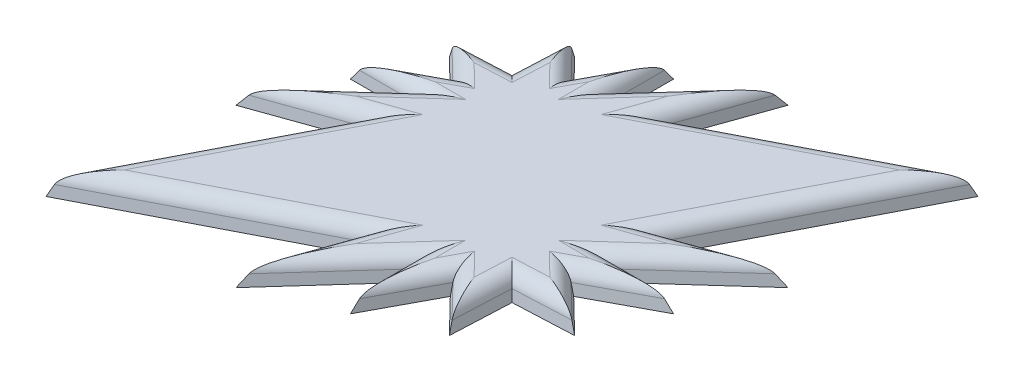
SolidWorks part; units mm, degrees
material "ABS"
ref_plane "Front Plane" through (0, 0, 0) normal (0, 0, 1) x (1, 0, 0)
ref_plane "Top Plane" through (0, 0, 0) normal (0, 1, 0) x (1, 0, 0)
ref_plane "Right Plane" through (0, 0, 0) normal (1, 0, 0) x (0, 0, -1)
sketch "Sketch1" plane through (0, 0, 0) normal (0, 1, 0) x (1, 0, 0)
  line L1 (-17.5, 17.5) -> (17.5, 17.5)
  line L2 (-17.5, 17.5) -> (-17.5, -17.5)
  line L3 (-17.5, -17.5) -> (17.5, -17.5)
  line L4 (17.5, 17.5) -> (17.5, -17.5)
  line L5 (-17.5, 17.5) -> (17.5, -17.5) construction
  line L6 (-17.5, -17.5) -> (17.5, 17.5) construction
  point P0 (0, 0)
  dimension "D1" = 35
sketch "Sketch2" plane through (0, 0, 0) normal (0, 1, 0) x (1, 0, 0)
  line L0 (0, 0) -> (15.1654, 15.1654) construction
  line L1 (-17.5, -17.5) -> (17.5, 17.5) construction
  line L2 (15.1654, 15.1654) -> (1.7587, 8.275)
  line L3 (1.7587, 8.275) -> (3.8411, 14.1232)
  line L4 (3.8411, 14.1232) -> (-1.3581, 8.3501)
  line L5 (-1.3581, 8.3501) -> (-1.3581, 11.8764)
  line L6 (-1.3581, 11.8764) -> (-3.6265, 7.6432)
  line L7 (-3.6265, 7.6432) -> (-5.8041, 9.8791)
  line L8 (-5.8041, 9.8791) -> (-5.982, 5.982)
  line L9 (-17.5, 17.5) -> (17.5, -17.5) construction
  line L10 (9.8791, -5.8041) -> (5.982, -5.982)
  line L11 (7.6432, -3.6265) -> (9.8791, -5.8041)
  line L12 (11.8764, -1.3581) -> (7.6432, -3.6265)
  line L13 (8.3501, -1.3581) -> (11.8764, -1.3581)
  line L14 (14.1232, 3.8411) -> (8.3501, -1.3581)
  line L15 (8.275, 1.7587) -> (14.1232, 3.8411)
  line L16 (15.1654, 15.1654) -> (8.275, 1.7587)
  line L17 (-17.5, 17.5) -> (17.5, -17.5) construction
  line L18 (5.8041, -9.8791) -> (5.982, -5.982)
  line L19 (3.6265, -7.6432) -> (5.8041, -9.8791)
  line L20 (1.3581, -11.8764) -> (3.6265, -7.6432)
  line L21 (1.3581, -8.3501) -> (1.3581, -11.8764)
  line L22 (-3.8411, -14.1232) -> (1.3581, -8.3501)
  line L23 (-1.7587, -8.275) -> (-3.8411, -14.1232)
  line L24 (-15.1654, -15.1654) -> (-1.7587, -8.275)
  line L25 (-15.1654, -15.1654) -> (-8.275, -1.7587)
  line L26 (-8.275, -1.7587) -> (-14.1232, -3.8411)
  line L27 (-14.1232, -3.8411) -> (-8.3501, 1.3581)
  line L28 (-8.3501, 1.3581) -> (-11.8764, 1.3581)
  line L29 (-11.8764, 1.3581) -> (-7.6432, 3.6265)
  line L30 (-7.6432, 3.6265) -> (-9.8791, 5.8041)
  line L31 (-9.8791, 5.8041) -> (-5.982, 5.982)
  circle A0 centre (0, 0) radius 8.4599 construction
extrude "Boss-Extrude1" add sketch "Sketch2" along normal blind 1.5 draft 10
fillet "Fillet1" radius 1 28 edges at (2.5933, 1.5, 9.0114) (1.6225, 1.5, 9.242) (-0.7607, 1.5, 10.3075) (-2.2147, 1.5, 10.3441) (-7.9195, 1.5, 11.144) (-11.144, 1.5, 7.9195) (-10.3441, 1.5, 2.2147) (-10.3075, 1.5, 0.7607) (-9.242, 1.5, -1.6225) (-9.0114, 1.5, -2.5933) (-8.2286, 1.5, -4.5658) (-7.4931, 1.5, -5.6483) (-5.6483, 1.5, -7.4931) (-4.5658, 1.5, -8.2286) (-2.5933, 1.5, -9.0114) (-1.6225, 1.5, -9.242) (0.7607, 1.5, -10.3075) (2.2147, 1.5, -10.3441) (7.9195, 1.5, -11.144) (11.144, 1.5, -7.9195) (10.3441, 1.5, -2.2147) (10.3075, 1.5, -0.7607) (9.242, 1.5, 1.6225) (9.0114, 1.5, 2.5933) (8.2286, 1.5, 4.5658) (7.4931, 1.5, 5.6483) (5.6483, 1.5, 7.4931) (4.5658, 1.5, 8.2286)
